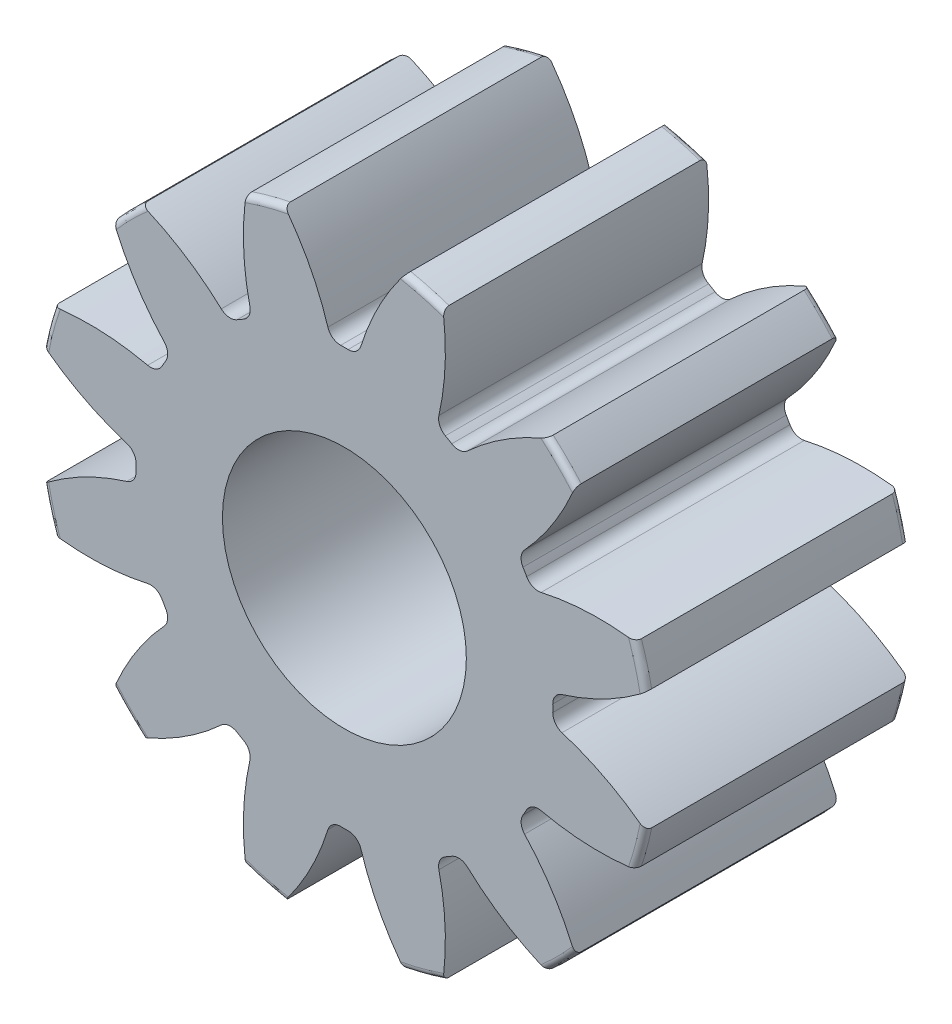
SolidWorks part; units mm, degrees
ref_plane "Front Plane" through (0, 0, 0) normal (0, 0, 1) x (1, 0, 0)
ref_plane "Top Plane" through (0, 0, 0) normal (0, 1, 0) x (1, 0, 0)
ref_plane "Right Plane" through (0, 0, 0) normal (1, 0, 0) x (0, 0, -1)
sketch "Sketch1" plane through (0, 0, 0) normal (0, 0, 1) x (1, 0, 0)
  line L0 (-152.4, 0) -> (152.4, 0) construction
  circle A0 centre (0, 0) radius 3.5 construction
  circle A1 centre (0, 0) radius 3 construction
  circle A2 centre (0, 0) radius 2.375 construction
  circle A3 centre (0, 0) radius 2.25 construction
  circle A4 centre (0, 0) radius 1 construction
  dimension "D2" = 0.5
  dimension "D3" = 1.125
  dimension "D1" = 1.125
sketch "Sketch2" plane through (0, 0, 0) normal (1, 0, 0) x (0, 0, -1)
  line L0 (0, 0) -> (-3, 0) construction
  line L1 (-3, 0) -> (-7, 0) construction
  dimension "Overall Width" = 7
  dimension "Face Width" = 3
sketch "Sketch4" plane through (0, 0, 0) normal (1, 0, 0) x (0, 0, -1)
  line L0 (-7, 1) -> (-7, 2.25)
  line L1 (-7, 2.25) -> (-3, 2.25)
  line L2 (-3, 2.25) -> (-3, 3.5)
  line L3 (-3, 3.5) -> (0, 3.5)
  line L4 (0, 3.5) -> (0, 1)
  line L5 (-3, 2.25) -> (-3, 0) construction
  line L6 (0, 3.5) -> (0, -3.5) construction
  line L7 (-3, 2.25) -> (0, 2.25) construction
  line L12 (-7, 1) -> (0, 1)
revolve "Revolve1" add sketch "Sketch4" angle 360 about L1
fillet "Fillet2" radius 0.07 4 edges at (0, 2.25, 7) (0, 2.25, 3) (0, 3.5, 3) (0, 3.5, 0)
sketch "Sketch7" plane through (0, 0, 3) normal (0, 0, 1) x (1, 0, 0)
  line L0 (0, 0) -> (0, 3.5) construction
  line L1 (0.3916, 2.9743) -> (0.635, 3.4419) construction
  line L3 (0.9059, 3.3807) -> (0.7765, 2.8978) construction
  line L4 (0.7765, 2.8978) -> (0.6147, 2.2941) construction
  line L5 (0, 0) -> (0.6147, 2.2941) construction
  line L6 (0.3916, 2.9743) -> (0, 0) construction
  line L7 (0.3916, 2.9743) -> (0.4568, 3.4701) construction
  line L8 (0.3916, 2.9743) -> (0, 0) construction
  circle A0 centre (0, 0) radius 3.5 construction
  arc A1 (-0.0421, 2.3746) -> (0.0421, 2.3746) centre (0, 0) cw
  circle A2 centre (0, 0) radius 2.375 construction
  arc A3 (-0.3916, 2.9743) -> (0.3916, 2.9743) centre (0, 0) cw construction
  circle A4 centre (0, 0) radius 3 construction
  arc A5 (1.1224, 3.3152) -> (0.6856, 3.4322) centre (0, 0) ccw construction
  arc A6 (0.3916, 2.9743) -> (1.148, 2.7716) centre (0, 0) cw construction
  arc A7 (-0.6856, 3.4322) -> (0.6856, 3.4322) centre (0, 0) cw
  arc A8 (0.188, 2.4801) -> (0.6856, 3.4322) centre (3.0526, 1.5891) cw
  arc A9 (-0.188, 2.4801) -> (-0.6856, 3.4322) centre (-3.0526, 1.5891) ccw
  arc A10 (-0.0421, 2.3746) -> (-0.188, 2.4801) centre (-0.0447, 2.5246) cw
  arc A11 (0.0421, 2.3746) -> (0.188, 2.4801) centre (0.0447, 2.5246) ccw
  point P26 (-0.156, 2.3699)
  point P29 (0.156, 2.3699)
  dimension "D4" = 0.15
  dimension "D5" = 3
  dimension "D3" = 20
  dimension "D1" = 1.5708
  dimension "D2" = 0.7854
extrude "Cut-Extrude2" cut sketch "Sketch7" against normal through all
pattern_circular "CirPattern1" count 12 over 360 about axis through (0, 0, 0) along (0, 0, 1) of "Cut-Extrude2"
sketch "Sketch8" plane through (0, 0, 7) normal (0, 0, 1) x (1, 0, 0)
  circle A0 centre (0, 0) radius 3.5
  arc A1 (1.1224, 3.3152) -> (0.6856, 3.4322) centre (0, 0) ccw construction
extrude "Cut-Extrude3" cut sketch "Sketch8" against normal up to surface (4 mm away) up to face at (0, 0, 3)
sketch "Sketch9" plane through (0, 0, 3) normal (0, 0, 1) x (1, 0, 0)
  circle A0 centre (0, 0) radius 1.39
  dimension "D1" = 2.78
extrude "Cut-Extrude4" cut sketch "Sketch9" against normal through all
equation "\"D1@Sketch1\"=2.25*(\"Pitch Dia.@Sketch1\"/\"Number of Teeth@Sketch1\")"
equation "\"D1@CirPattern1\"=\"Number of Teeth@Sketch1\""
equation "\"D1@Fillet2\"=\"OD@Sketch1\"*.01"
equation "\"D1@Sketch7\"=3.14159*(\"Pitch Dia.@Sketch1\"/\"Number of Teeth@Sketch1\")"
equation "\"D2@Sketch7\"=\"D1@Sketch7\"/2"
equation "\"D4@Sketch7\"=\"D1@Sketch7\"*.0955"
equation "\"D5@Sketch7\"=\"Pitch Dia.@Sketch1\"/2"
